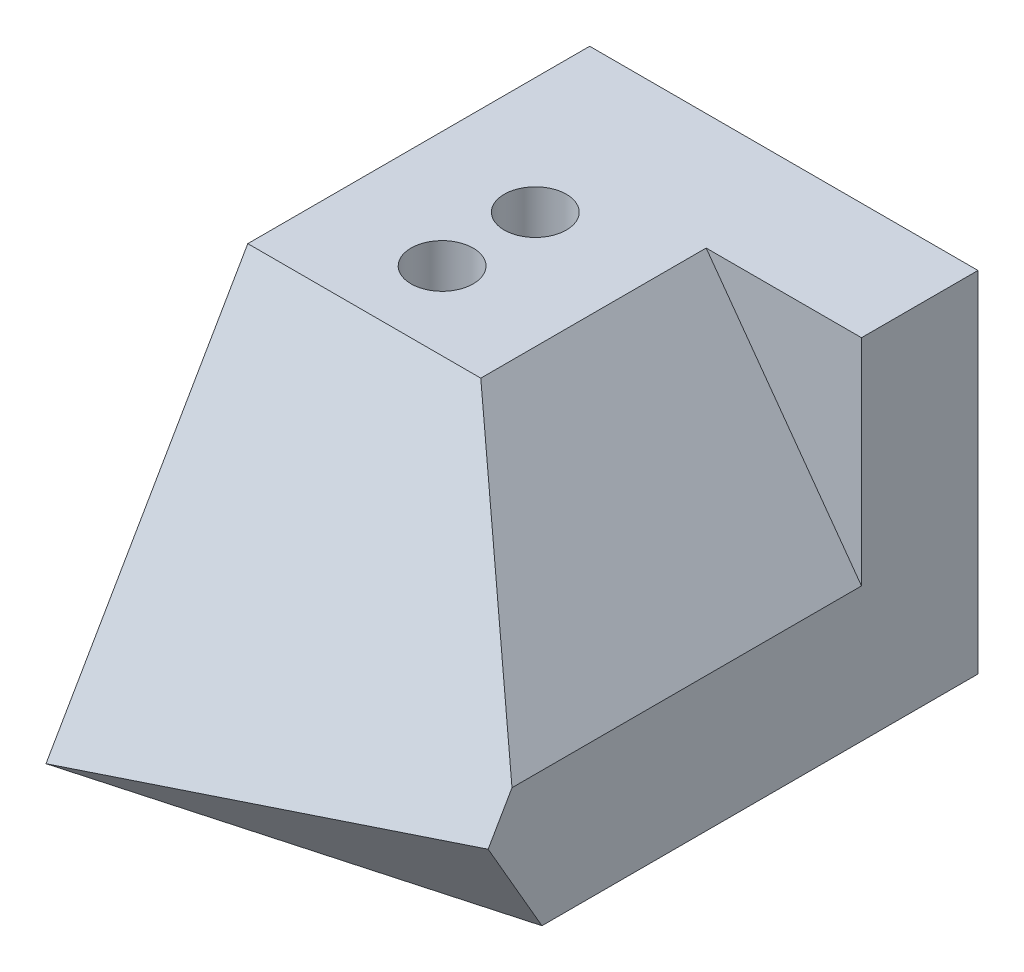
SolidWorks part; units mm, degrees
material "1060 Alloy"
ref_plane "Front Plane" through (0, 0, 0) normal (0, 0, 1) x (1, 0, 0)
ref_plane "Top Plane" through (0, 0, 0) normal (0, 1, 0) x (1, 0, 0)
ref_plane "Right Plane" through (0, 0, 0) normal (1, 0, 0) x (0, 0, -1)
sketch "Sketch1" plane through (0, 0, 0) normal (0, 0, 1) x (1, 0, 0)
  line L1 (0, 45) -> (50, 45)
  line L2 (0, 45) -> (0, 0)
  line L3 (0, 0) -> (50, 0)
  line L4 (50, 45) -> (50, 0)
  dimension "D1" = 50
  dimension "D2" = 45
extrude "Boss-Extrude1" add sketch "Sketch1" along normal mid plane 70
sketch "Sketch3" plane through (0, 0, 0) normal (1, 0, 0) x (0, 0, -1)
  line L0 (-35, 0) -> (-9.0192, 45)
  line L4 (35, 0) -> (35, 45)
  line L5 (35, 45) -> (-35, 45)
  line L6 (-35, 45) -> (-35, 0)
  line L7 (-35, 0) -> (35, 0)
  line L8 (35, 0) -> (35, 45)
  line L9 (35, 45) -> (-35, 45)
  line L10 (-35, 45) -> (-35, 0)
  line L11 (-35, 0) -> (35, 0)
  point P7 (0, 0)
  dimension "D2" = 30
  dimension "D1" = 0
extrude "Cut-Extrude1" cut sketch "Sketch3" along normal through all contours L9 L10 L0
ref_plane "Plane2" through (50, 0, 0) normal (1, 0, 0) x (0, 0, -1)
sketch "Sketch8" plane through (50, 0, 0) normal (1, 0, 0) x (0, 0, -1)
  line L0 (-28.0718, 12) -> (-21.1436, 0)
  line L4 (-9.0192, 45) -> (-35, 0)
  line L5 (-35, 0) -> (35, 0)
  line L6 (35, 0) -> (35, 45)
  line L7 (35, 45) -> (-9.0192, 45)
  line L8 (-9.0192, 45) -> (-35, 0)
  line L9 (-35, 0) -> (35, 0)
  line L10 (35, 0) -> (35, 45)
  line L11 (35, 45) -> (-9.0192, 45)
  dimension "D2" = 12
  dimension "D3" = 120
  dimension "D1" = 0
ref_plane "Plane3" through (0, 15.1554, 26.25) normal (0, 0.5, 0.866) x (1, 0, 0)
sketch "Sketch9" plane through (0, 15.1554, 26.25) normal (0, 0.5, 0.866) x (1, 0, 0)
  line L0 (50, -3.6436) -> (0, -17.5)
  line L4 (0, 34.4615) -> (0, -17.5)
  line L5 (0, -17.5) -> (50, -17.5)
  line L6 (50, -17.5) -> (50, 34.4615)
  line L7 (50, 34.4615) -> (0, 34.4615)
  line L8 (0, 34.4615) -> (0, -17.5)
  line L9 (0, -17.5) -> (50, -17.5)
  line L10 (50, -17.5) -> (50, 34.4615)
  line L11 (50, 34.4615) -> (0, 34.4615)
  dimension "D1" = 0
extrude "Cut-Extrude2" cut sketch "Sketch9" along direction (0, -0.866, -0.5) on the side against the normal blind 70 contours L9 L10 L0
ref_plane "Plane4" through (0, 0, -20) normal (0, 0, 1) x (1, 0, 0)
sketch "Sketch10" plane through (0, 15.1554, 26.25) normal (0, 0.5, 0.866) x (1, 0, 0)
  line L0 (30, 34.4615) -> (50, 2.5)
  line L4 (0, -17.5) -> (50, -3.6436)
  line L5 (50, -3.6436) -> (50, 34.4615)
  line L6 (50, 34.4615) -> (0, 34.4615)
  line L7 (0, 34.4615) -> (0, -17.5)
  line L8 (0, -17.5) -> (50, -3.6436)
  line L9 (50, -3.6436) -> (50, 34.4615)
  line L10 (50, 34.4615) -> (0, 34.4615)
  line L11 (0, 34.4615) -> (0, -17.5)
  point P6 (0, 0)
  dimension "D2" = 30
  dimension "D3" = 20
  dimension "D1" = 0
sketch "Sketch20" plane through (0, 0, 0) normal (0, 1, 0) x (1, 0, 0)
  line L0 (15, -9.0192) -> (15, 35) construction
  line L6 (30, -9.0192) -> (30, 20)
  line L7 (30, 20) -> (50, 20)
  line L8 (50, 20) -> (50, 35)
  line L9 (50, 35) -> (0, 35)
  line L10 (0, 35) -> (0, -9.0192)
  line L11 (0, -9.0192) -> (30, -9.0192)
  line L12 (30, -9.0192) -> (30, 20)
  line L13 (30, 20) -> (50, 20)
  line L14 (50, 20) -> (50, 35)
  line L15 (50, 35) -> (0, 35)
  line L16 (0, 35) -> (0, -9.0192)
  line L17 (0, -9.0192) -> (30, -9.0192)
  circle A0 centre (15, 13) radius 4
  circle A1 centre (15, 1) radius 4
  point P6 (15, 1)
  point P8 (15, 13)
  dimension "D2" = 22
  dimension "D3" = 12
  dimension "D1" = 0
extrude "Cut-Extrude5" cut sketch "Sketch20" along normal through all contours A0 | A1
sketch "Sketch23" plane through (0, 0, -20) normal (0, 0, 1) x (1, 0, 0)
  line L0 (30, 45) -> (50, 17.3205) construction
  line L1 (30, 45) -> (50, 17.3205)
  line L4 (0, 0) -> (50, 12)
  line L5 (50, 12) -> (50, 45)
  line L6 (50, 45) -> (0, 45)
  line L7 (0, 45) -> (0, 0)
  line L8 (0, 0) -> (50, 12)
  line L9 (50, 12) -> (50, 45)
  line L10 (50, 45) -> (0, 45)
  line L11 (0, 45) -> (0, 0)
  dimension "D1" = 0
extrude "Cut-Extrude6" cut sketch "Sketch23" along normal through all contours L9 L10 L1
